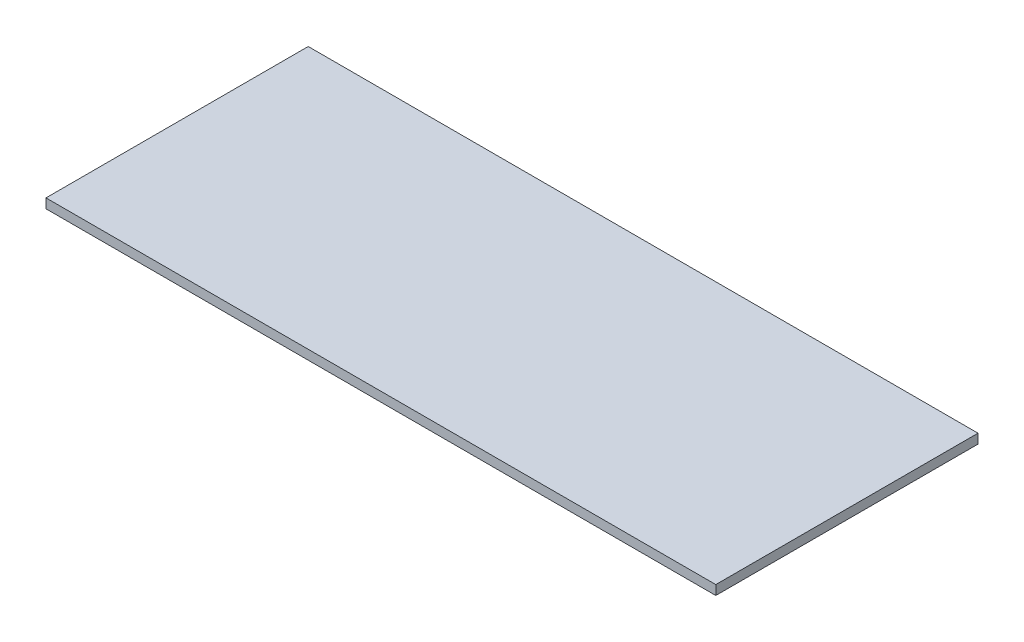
SolidWorks part; units mm, degrees
ref_plane "Front Plane" through (0, 0, 0) normal (0, 0, 1) x (1, 0, 0)
ref_plane "Top Plane" through (0, 0, 0) normal (0, 1, 0) x (1, 0, 0)
ref_plane "Right Plane" through (0, 0, 0) normal (1, 0, 0) x (0, 0, -1)
sketch "Sketch1" plane through (0, 0, 0) normal (0, 1, 0) x (1, 0, 0)
  line L1 (-673.1, -263.525) -> (673.1, -263.525)
  line L2 (-673.1, -263.525) -> (-673.1, 263.525)
  line L3 (-673.1, 263.525) -> (673.1, 263.525)
  line L4 (673.1, -263.525) -> (673.1, 263.525)
  line L5 (-673.1, -263.525) -> (673.1, 263.525) construction
  line L6 (-673.1, 263.525) -> (673.1, -263.525) construction
  point P0 (0, 0)
  dimension "D1" = 1346.2
  dimension "D2" = 527.05
extrude "Boss-Extrude1" add sketch "Sketch1" along normal blind 19.05
